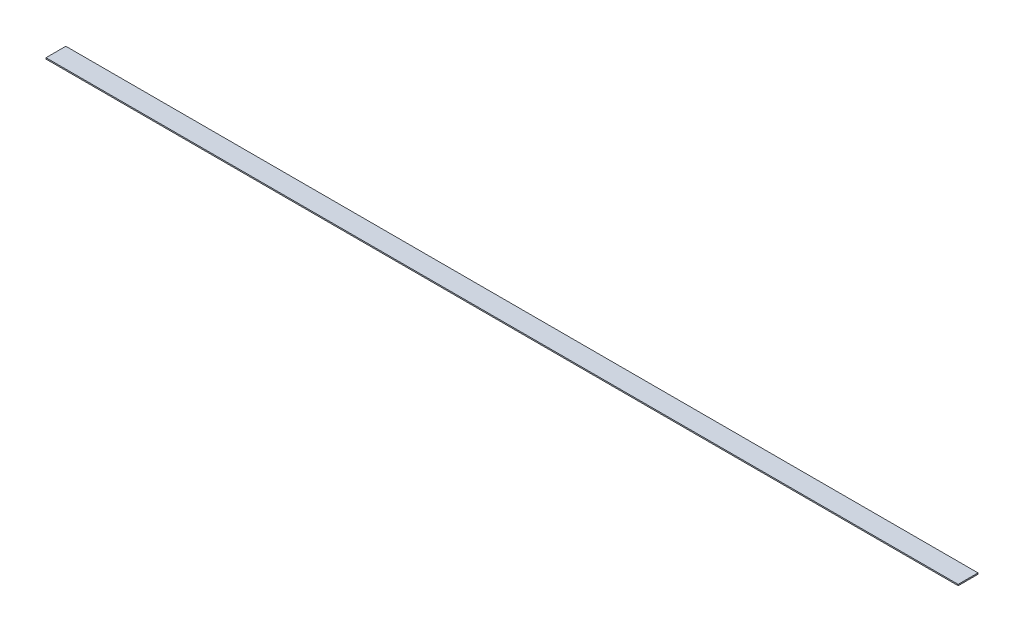
SolidWorks part; units mm, degrees
material "Nylon 101"
ref_plane "Front Plane" through (0, 0, 0) normal (0, 0, 1) x (1, 0, 0)
ref_plane "Top Plane" through (0, 0, 0) normal (0, 1, 0) x (1, 0, 0)
ref_plane "Right Plane" through (0, 0, 0) normal (1, 0, 0) x (0, 0, -1)
sketch "Sketch1" plane through (0, 0, 0) normal (0, 1, 0) x (1, 0, 0)
  line L1 (0, 0) -> (1168.4, 0)
  line L2 (0, 0) -> (0, 25.4)
  line L3 (0, 25.4) -> (1168.4, 25.4)
  line L4 (1168.4, 0) -> (1168.4, 25.4)
  dimension "D1" = 25.4
  dimension "D2" = 1168.4
extrude "Boss-Extrude1" add sketch "Sketch1" along normal blind 1.5875
